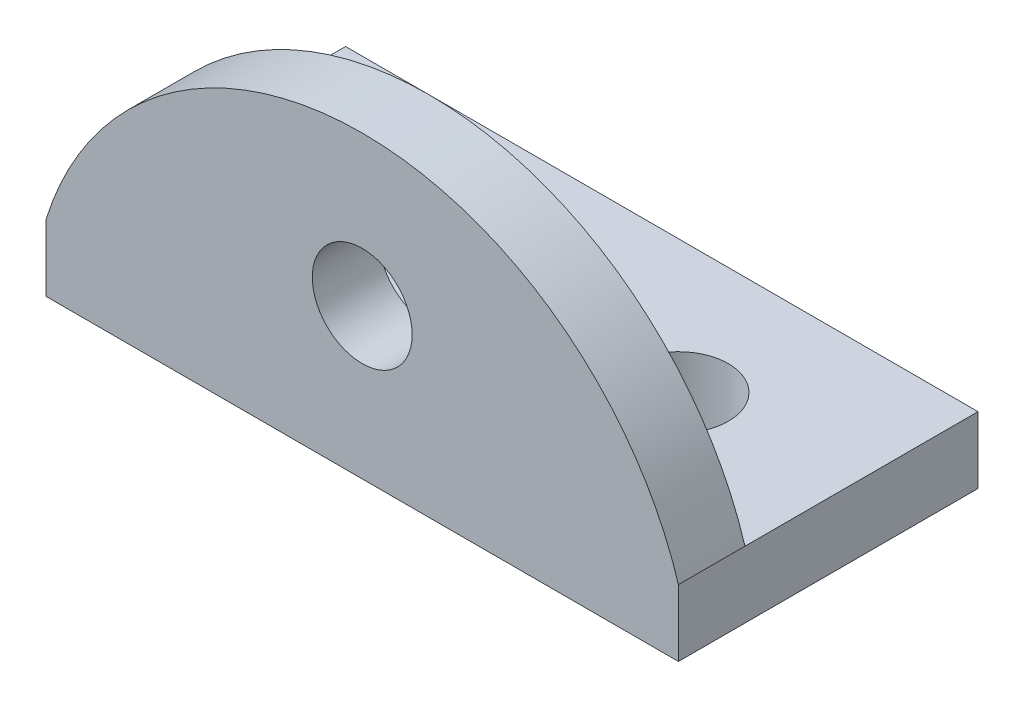
SolidWorks part; units mm, degrees
ref_plane "Front Plane" through (0, 0, 0) normal (0, 0, 1) x (1, 0, 0)
ref_plane "Top Plane" through (0, 0, 0) normal (0, 1, 0) x (1, 0, 0)
ref_plane "Right Plane" through (0, 0, 0) normal (1, 0, 0) x (0, 0, -1)
sketch "Sketch1" plane through (0, 0, 0) normal (0, 1, 0) x (1, 0, 0)
  line L1 (0, 0) -> (19, 0)
  line L2 (0, 0) -> (0, 9)
  line L3 (0, 9) -> (19, 9)
  line L4 (19, 0) -> (19, 9)
  dimension "D1" = 19
  dimension "D2" = 9
extrude "Boss-Extrude1" add sketch "Sketch1" along normal blind 2
sketch "Sketch3" plane through (0, 0, 0) normal (0, 0, 1) x (1, 0, 0)
  line L0 (0, 0) -> (19, 0) construction
  line L1 (0, 2) -> (19, 2)
  arc A0 (0, 2) -> (19, 2) centre (9.5, -0.9464) cw
  point P3 (9.5, 9)
  dimension "D1" = 9
extrude "Boss-Extrude2" add sketch "Sketch3" against normal blind 2
sketch "Sketch4" plane through (0, 2, 0) normal (0, 1, 0) x (1, 0, 0)
  line L0 (19, 9) -> (0, 9) construction
  line L3 (9.5, 9) -> (9.5, 0) construction
  line L4 (19, 9) -> (0, 9) construction
  line L5 (0, 0) -> (19, 0) construction
  circle A0 centre (5, 5) radius 1.5
  circle A1 centre (14, 5) radius 1.5
  dimension "D2" = 3
  dimension "D3" = 3
  dimension "D1" = 4.5
  dimension "D4" = 4
  dimension "D5" = 4
  dimension "D6" = 4.5
extrude "Cut-Extrude1" cut sketch "Sketch4" against normal blind 2
sketch "Sketch5" plane through (0, 0, 0) normal (0, 0, 1) x (1, 0, 0)
  line L0 (9.5, 0) -> (9.5, 9) construction
  line L1 (0, 0) -> (19, 0) construction
  circle A0 centre (9.5, 4.5) radius 1.5
  arc A1 (19, 2) -> (0, 2) centre (9.5, -0.9464) ccw construction
  dimension "D1" = 3
  dimension "D2" = 4.5
extrude "Cut-Extrude2" cut sketch "Sketch5" against normal blind 2 contours A0
